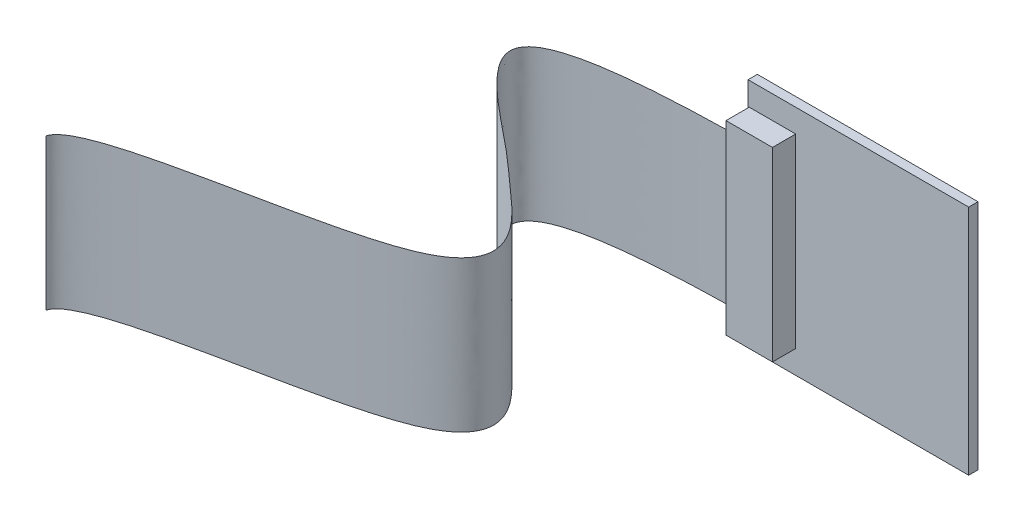
SolidWorks part; units mm, degrees
ref_plane "Front Plane" through (0, 0, 0) normal (0, 0, 1) x (1, 0, 0)
ref_plane "Top Plane" through (0, 0, 0) normal (0, 1, 0) x (1, 0, 0)
ref_plane "Right Plane" through (0, 0, 0) normal (1, 0, 0) x (0, 0, -1)
sketch "Sketch1" plane through (0, 0, 0) normal (0, 0, 1) x (1, 0, 0)
  line L1 (-12.065, -12.7) -> (12.065, -12.7)
  line L2 (-12.065, -12.7) -> (-12.065, 12.7)
  line L3 (-12.065, 12.7) -> (12.065, 12.7)
  line L4 (12.065, -12.7) -> (12.065, 12.7)
  line L5 (-12.065, -12.7) -> (12.065, 12.7) construction
  line L6 (-12.065, 12.7) -> (12.065, -12.7) construction
  point P0 (0, 0)
  dimension "D1" = 24.13
  dimension "D2" = 25.4
extrude "Boss-Extrude1" add sketch "Sketch1" along normal blind 1.016
sketch "Sketch2" plane through (0, 0, 1.016) normal (0, 0, 1) x (1, 0, 0)
  line L0 (-12.065, 12.7) -> (-12.065, -12.7) construction
  line L1 (-11.938, -10.16) -> (-6.858, -10.16)
  line L2 (-11.938, -10.16) -> (-11.938, 10.16)
  line L3 (-11.938, 10.16) -> (-6.858, 10.16)
  line L4 (-6.858, -10.16) -> (-6.858, 10.16)
  line L5 (-11.938, -10.16) -> (-6.858, 10.16) construction
  line L6 (-11.938, 10.16) -> (-6.858, -10.16) construction
  point P0 (-9.398, 0)
  dimension "D1" = 20.32
  dimension "D2" = 5.08
  dimension "D3" = 0.127
extrude "Boss-Extrude2" add sketch "Sketch2" along normal blind 2.54 separate body
sketch "Sketch3" plane through (0, 0, 0) normal (0, 0, -1) x (-1, 0, 0)
  line L0 (12.065, 12.7) -> (12.065, -12.7) construction
  line L1 (6.985, 3.81) -> (-0.635, 3.81)
  line L2 (6.985, 3.81) -> (6.985, -3.81)
  line L3 (6.985, -3.81) -> (-0.635, -3.81)
  line L4 (-0.635, 3.81) -> (-0.635, -3.81)
  line L5 (6.985, 3.81) -> (-0.635, -3.81) construction
  line L6 (6.985, -3.81) -> (-0.635, 3.81) construction
  line L7 (-12.065, 12.7) -> (12.065, 12.7) construction
  point P0 (3.175, 0)
  dimension "D1" = 7.62
  dimension "D2" = 7.62
  dimension "D3" = 5.08
  dimension "D4" = 8.89
extrude "Boss-Extrude3" add sketch "Sketch3" along normal blind 3.81
sketch "Sketch5" plane through (0, 0, -3.81) normal (0, 0, -1) x (-1, 0, 0)
  line L0 (6.985, 3.81) -> (-0.635, 3.81) construction
  line L1 (6.985, -3.81) -> (6.985, 3.81) construction
  circle A0 centre (3.175, 0) radius 3.7465
  dimension "D1" = 7.493
  dimension "D2" = 3.81
  dimension "D3" = 3.81
extrude "Boss-Extrude4" add sketch "Sketch5" along normal blind 1.778
sketch "Sketch6" plane through (0, 0, 0) normal (0, 0, -1) x (-1, 0, 0)
  line L0 (-12.065, -12.7) -> (-12.065, 12.7) construction
  line L1 (-5.461, 3.81) -> (-10.541, 3.81)
  line L2 (-5.461, 3.81) -> (-5.461, -3.81)
  line L3 (-5.461, -3.81) -> (-10.541, -3.81)
  line L4 (-10.541, 3.81) -> (-10.541, -3.81)
  line L5 (-5.461, 3.81) -> (-10.541, -3.81) construction
  line L6 (-5.461, -3.81) -> (-10.541, 3.81) construction
  point P0 (-8.001, 0)
  dimension "D1" = 1.524
  dimension "D2" = 5.08
  dimension "D3" = 7.62
  dimension "D4" = 0
extrude "Boss-Extrude5" add sketch "Sketch6" along normal blind 1.27
sketch "Sketch7" plane through (-11.938, 0, 0) normal (-1, 0, 0) x (0, 0, 1)
  line L0 (2.4561, 8.255) -> (2.4561, -8.255)
  line L1 (0, 12.7) -> (0, -12.7) construction
  point P2 (0, 0)
  dimension "D1" = 16.51
  dimension "D2" = 8.255
sketch3d "3DSketch1"
  line L0 (-11.938, 8.255, 2.4561) -> (-11.938, -8.255, 2.4561) construction
  spline S0 degree 3 poles (-11.938, 8.255, 2.4561) (-26.1758, 8.255, 2.7258) (-37.6882, 8.255, 4.9205) (-22.2332, 8.255, 16.9636) (-19.8036, 8.255, 19.5802) (-4.1763, 8.255, 32.4272) (-48.6542, 8.255, 36.5242) (-49.5685, 8.255, 40.2878) knots 0 0 0 0 0.18308 0.309256 0.468446 0.731342 1 1 1 1
surface "Surface-Extrude1" sketch "3DSketch1" parameters "D1"=16.51
sketch "Sketch8" plane through (0, 0, -5.588) normal (0, 0, -1) x (-1, 0, 0)
  line L1 (2.2225, 0.9525) -> (4.1275, 0.9525)
  line L2 (2.2225, 0.9525) -> (2.2225, -0.9525)
  line L3 (2.2225, -0.9525) -> (4.1275, -0.9525)
  line L4 (4.1275, 0.9525) -> (4.1275, -0.9525)
  line L5 (2.2225, 0.9525) -> (4.1275, -0.9525) construction
  line L6 (2.2225, -0.9525) -> (4.1275, 0.9525) construction
  point P0 (3.175, 0)
  dimension "D1" = 1.905
  dimension "D2" = 1.905
surface "Surface-Extrude2" sketch "Sketch8" parameters "D1"=50.8, "D3"=27
